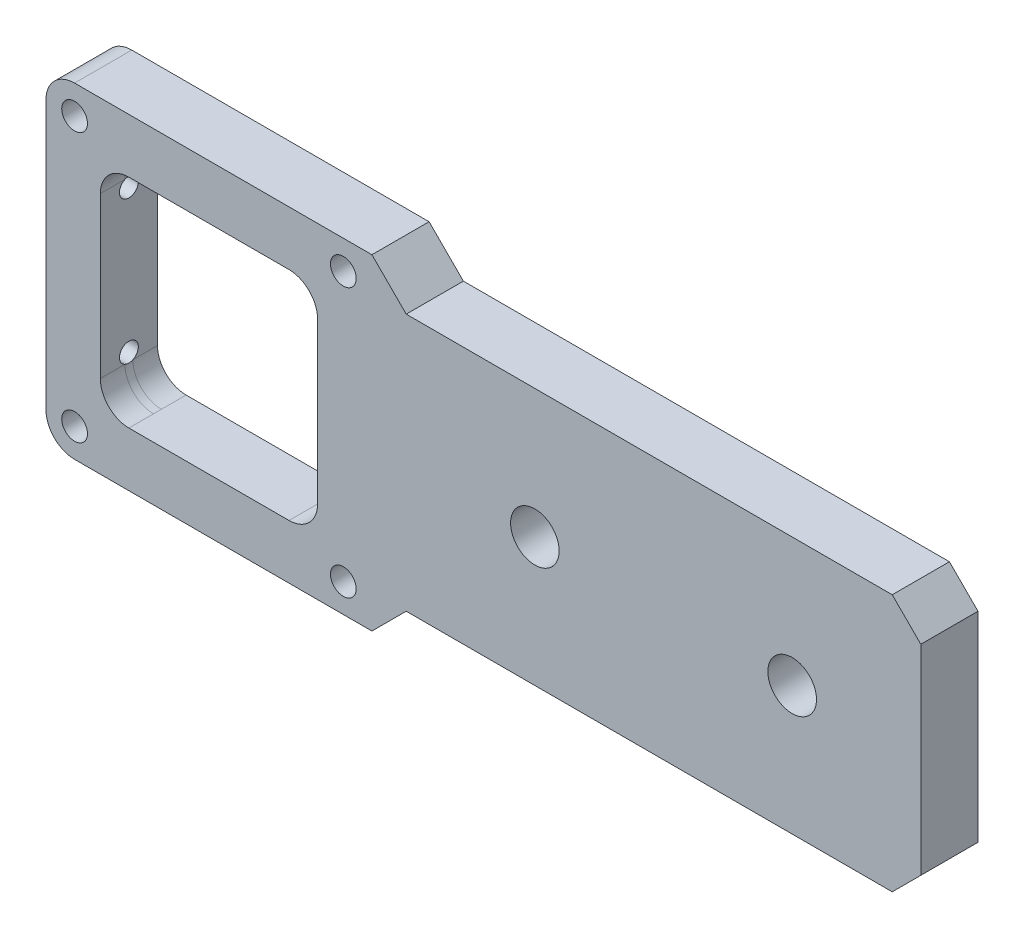
SolidWorks part; units mm, degrees
material "6061 合金"
ref_plane "前视基准面" through (0, 0, 0) normal (0, 0, 1) x (1, 0, 0)
ref_plane "上视基准面" through (0, 0, 0) normal (0, 1, 0) x (1, 0, 0)
ref_plane "右视基准面" through (0, 0, 0) normal (1, 0, 0) x (0, 0, -1)
sketch "草图1" plane through (0, 0, 0) normal (0, 0, 1) x (1, 0, 0)
  line L0 (28.5, -28.5) -> (34.5, -22.5)
  line L1 (-28.5, -28.5) -> (28.5, -28.5)
  line L2 (-28.5, -28.5) -> (-28.5, 28.5)
  line L3 (-28.5, 28.5) -> (28.5, 28.5)
  line L4 (28.5, -28.5) -> (28.5, 28.5)
  line L5 (-28.5, -28.5) -> (28.5, 28.5) construction
  line L6 (-28.5, 28.5) -> (28.5, -28.5) construction
  line L7 (124.5, -22.5) -> (28.5, -22.5)
  line L8 (124.5, -22.5) -> (124.5, 22.5)
  line L9 (124.5, 22.5) -> (28.5, 22.5)
  line L10 (28.5, -22.5) -> (28.5, 22.5)
  line L11 (124.5, -22.5) -> (28.5, 22.5) construction
  line L12 (124.5, 22.5) -> (28.5, -22.5) construction
  line L13 (124.5, 0) -> (-55.3636, 0) construction
  line L14 (28.5, 28.5) -> (34.5, 22.5)
  point P0 (0, 0)
  point P6 (76.5, 0)
  dimension "D1" = 63
  dimension "D2" = 57
  dimension "D3" = 45
  dimension "D4" = 90
  dimension "D5" = 45
extrude "凸台-拉伸1" add sketch "草图1" along normal mid plane 10
sketch "草图6" plane through (0, 0, 5) normal (0, 0, 1) x (1, 0, 0)
  circle A0 centre (0, 0) radius 10
  dimension "D1" = 20
extrude "过孔" cut sketch "草图6" against normal blind 10
sketch "草图19" plane through (0, 0, -5) normal (0, 0, -1) x (-1, 0, 0)
  circle A0 centre (0, 0) radius 12
  dimension "D1" = 24
extrude "轴承孔" cut sketch "草图19" against normal blind 5
hole_wizard "Ø8.5 (8.5) 直径孔1" positions "草图5" profile "草图4" hole size "Ø8.5" standard "GB" end condition through all
sketch "草图5" plane through (0, 0, 5) normal (0, 0, 1) x (1, 0, 0)
  line L1 (79.5, -22.5) -> (79.5, 22.5) construction
  line L2 (124.5, -22.5) -> (34.5, -22.5) construction
  line L3 (124.5, 22.5) -> (34.5, 22.5) construction
  line L5 (0, 0) -> (120.0042, 0) construction
  point P0 (57, 0)
  point P3 (102, 0)
  dimension "D1" = 45
sketch "草图4" plane through (57, 0, 5) normal (1, 0, 0) x (0, -1, 0)
  line L0 (0, 0) -> (0, 10)
  line L1 (0, 10) -> (4.25, 10)
  line L2 (4.25, 10) -> (4.25, 0)
  line L5 (4.25, 0) -> (0, 0)
  line L11 (0, -6.35) -> (0, 107.95) construction
  dimension "通孔孔直径" = 8.5
  dimension "通孔孔深度" = 10
hole_wizard "打孔尺寸(%根据)内六角圆柱头螺钉的类型1" positions "草图12" profile "草图11" counterbore size "M4" standard "GB" end condition through all
sketch "草图12" plane through (0, 0, -5) normal (0, 0, -1) x (-1, 0, 0)
  line L0 (0, 0) -> (0, -49.1013) construction
  line L2 (0, 0) -> (52.852, 0) construction
  point P0 (-23.5, 23.5)
  point P3 (23.5, 23.5)
  point P6 (23.5, -23.5)
  point P9 (-23.5, -23.5)
  dimension "D1" = 47
  dimension "D2" = 47
sketch "草图11" plane through (23.5, 23.5, -5) normal (1, 0, 0) x (0, 1, 0)
  line L0 (0, 0) -> (0, 10)
  line L1 (0, 10) -> (2.25, 10)
  line L3 (2.25, 10) -> (2.25, 4.6)
  line L4 (2.25, 4.6) -> (4, 4.6)
  line L5 (4, 4.6) -> (4, 0)
  line L7 (4, 0) -> (0, 0)
  line L11 (0, -6.35) -> (0, 107.95) construction
  dimension "通孔孔直径" = 4.5
  dimension "通孔孔深度" = 10
  dimension "柱形沉头孔直径" = 8
  dimension "柱形沉头孔深度" = 4.6
fillet "圆角1" radius 5 2 edges at (-28.5, 28.5, 0) (-28.5, -28.5, 0)
chamfer "倒角1" distance 5 angle 45 2 edges at (124.5, 22.5, 0) (124.5, -22.5, 0)
chamfer "倒角2" distance 0.2 angle 45 1 edges at (-12, 0, -5)
hole_wizard "M4 螺纹孔1" positions "草图21" profile "草图20" tap size "M4" standard "GB"
sketch "草图21" plane through (-28.5, 0, 0) normal (-1, 0, 0) x (0, 0, 1)
  line L0 (0, 0) -> (17.4295, 0) construction
  line L2 (0, 28.5) -> (0, -28.5) construction
  line L3 (-5, 28.5) -> (5, 28.5) construction
  line L4 (5, -28.5) -> (-5, -28.5) construction
  point P0 (0, 12.5)
  point P2 (0, -12.5)
  dimension "D1" = 25
sketch "草图20" plane through (-28.5, 12.5, 0) normal (0, 1, 0) x (0, 0, 1)
  line L0 (0, 0) -> (0, 15.5)
  line L1 (0, 15.5) -> (1.65, 15.5)
  line L2 (1.65, 15.5) -> (1.65, 0.2165)
  line L3 (1.65, 0.2165) -> (2.025, 0)
  line L5 (2.025, 0) -> (0, 0)
  line L6 (-1.65, 0.2165) -> (-2.025, 0) construction
  line L10 (0, 15.5) -> (-1.65, 15.5) construction
  line L11 (0, -6.35) -> (0, 107.95) construction
  dimension "螺纹孔钻头直径" = 3.3
  dimension "螺纹孔钻头深度" = 15.5
  dimension "近端锥形沉头孔直径" = 4.05
  dimension "近端锥形沉头孔角度" = 120
  dimension "导头角度" = 180
cosmetic thread "孔螺蚊线1" parameters "D1"=12, "D2"=4
cosmetic thread "孔螺蚊线2" parameters "D1"=12, "D2"=4
sketch "草图22" plane through (0, 0, -5) normal (0, 0, -1) x (-1, 0, 0)
  line L1 (-19, -19) -> (19, -19)
  line L2 (-19, -19) -> (-19, 19)
  line L3 (-19, 19) -> (19, 19)
  line L4 (19, -19) -> (19, 19)
  line L5 (-19, -19) -> (19, 19) construction
  line L6 (-19, 19) -> (19, -19) construction
  point P0 (0, 0)
  dimension "D1" = 38
  dimension "D2" = 38
extrude "切除-拉伸1" cut sketch "草图22" against normal blind 10
fillet "圆角2" radius 5 4 edges at (19, -19, 0) (-19, -19, 0) (-19, 19, 0) (19, 19, 0)
